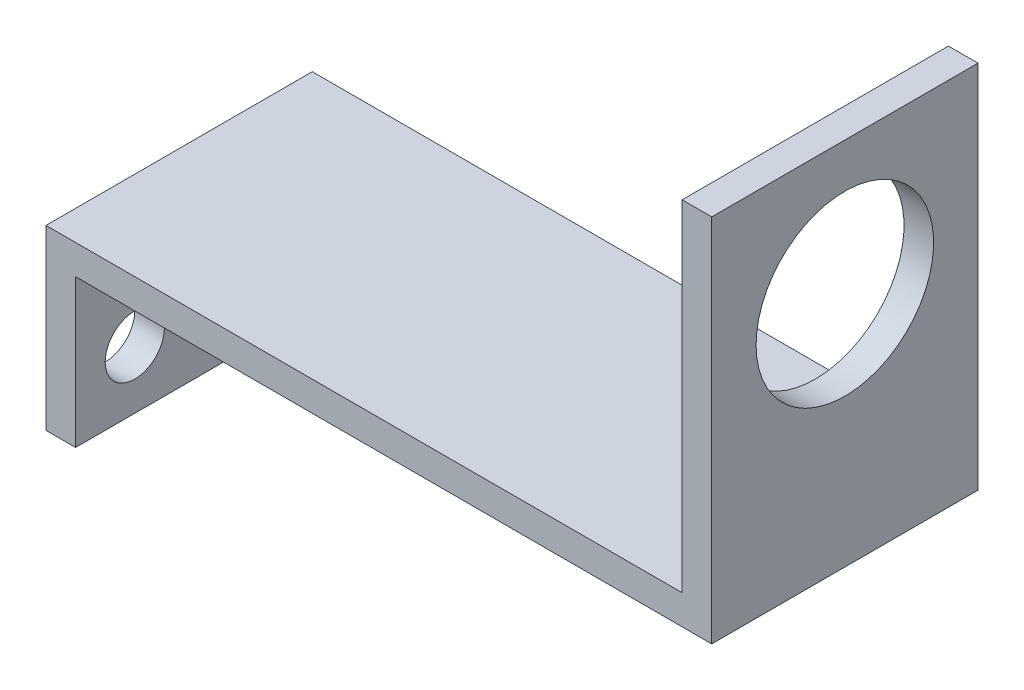
SolidWorks part; units mm, degrees
material "7075-T6 (SN)"
ref_plane "Front Plane" through (0, 0, 0) normal (0, 0, 1) x (1, 0, 0)
ref_plane "Top Plane" through (0, 0, 0) normal (0, 1, 0) x (1, 0, 0)
ref_plane "Right Plane" through (0, 0, 0) normal (1, 0, 0) x (0, 0, -1)
sketch "Sketch1" plane through (0, 0, 0) normal (0, 0, 1) x (1, 0, 0)
  line L0 (0, 0) -> (0, 12)
  line L1 (0, 12) -> (43, 12)
  line L2 (43, 12) -> (43, 35)
  line L3 (43, 35) -> (45, 35)
  line L4 (45, 35) -> (45, 10)
  line L5 (45, 10) -> (2, 10)
  line L6 (2, 10) -> (2, 0)
  line L7 (2, 0) -> (0, 0)
  dimension "D1" = 12
  dimension "D2" = 43
  dimension "D3" = 23
  dimension "D4" = 2
  dimension "D5" = 2
  dimension "D6" = 2
extrude "Boss-Extrude1" add sketch "Sketch1" along normal blind 18
sketch "Sketch2" plane through (0, 0, 0) normal (-1, 0, 0) x (0, 0, 1)
  line L0 (-3.4381, 4) -> (23.8691, 4) construction
  line L1 (4, -1.2191) -> (4, 10.9175) construction
  line L2 (14, -1.2191) -> (14, 10.9175) construction
  line L3 (18, 0) -> (0, 0) construction
  line L4 (0, 12) -> (0, 0) construction
  line L5 (18, 12) -> (18, 0) construction
  circle A0 centre (4, 4) radius 2
  circle A1 centre (14, 4) radius 2
  dimension "D4" = 4
  dimension "D5" = 4
  dimension "D1" = 4
  dimension "D2" = 4
  dimension "D3" = 4
extrude "Cut-Extrude1" cut sketch "Sketch2" against normal up to next
sketch "Sketch3" plane through (43, 0, 0) normal (-1, 0, 0) x (0, 0, 1)
  line L0 (9, 38.548) -> (9, 16.8086) construction
  line L1 (18, 35) -> (0, 35) construction
  circle A0 centre (9, 26) radius 6
  point P4 (9, 35)
  dimension "D1" = 12
  dimension "D2" = 9
extrude "Cut-Extrude2" cut sketch "Sketch3" against normal up to next
